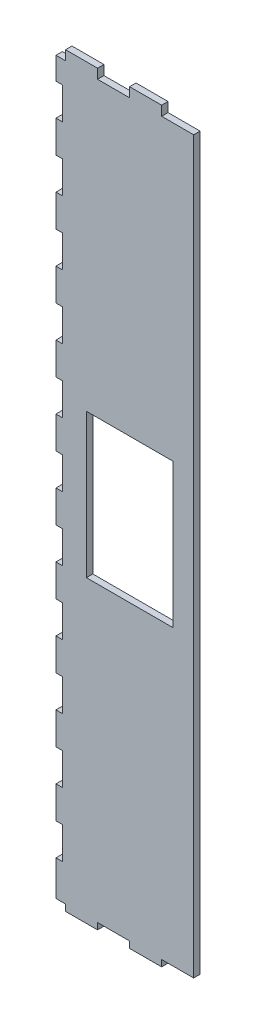
SolidWorks part; units mm, degrees
ref_plane "Front Plane" through (0, 0, 0) normal (0, 0, 1) x (1, 0, 0)
ref_plane "Top Plane" through (0, 0, 0) normal (0, 1, 0) x (1, 0, 0)
ref_plane "Right Plane" through (0, 0, 0) normal (1, 0, 0) x (0, 0, -1)
sketch "Sketch1" plane through (0, 0, 0) normal (0, 0, 1) x (1, 0, 0)
  line L1 (0, 0) -> (40, 0)
  line L2 (0, 0) -> (0, 227)
  line L3 (0, 227) -> (40, 227)
  line L4 (40, 0) -> (40, 227)
  dimension "D1" = 40
  dimension "D2" = 227
extrude "Boss-Extrude1" add sketch "Sketch1" along normal blind 2
sketch "Sketch2" plane through (0, 0, 0) normal (0, -1, 0) x (1, 0, 0)
  line L0 (0, 0) -> (40, 0) construction
  line L1 (30, 0) -> (20, 0)
  line L2 (30, 0) -> (30, 2)
  line L3 (30, 2) -> (20, 2)
  line L4 (20, 0) -> (20, 2)
  line L5 (0, 2) -> (40, 2) construction
  line L6 (40, 2) -> (40, 0) construction
  dimension "D1" = 10
  dimension "D2" = 10
extrude "Boss-Extrude2" add sketch "Sketch2" along normal blind 3
pattern_linear "LPattern1" count 2 spacing 20 along (-1, 0, 0) of "Boss-Extrude2"
sketch "Sketch3" plane through (0, 227, 0) normal (0, 1, 0) x (1, 0, 0)
  line L0 (40, -2) -> (0, -2) construction
  line L1 (30, -2) -> (20, -2)
  line L2 (30, -2) -> (30, 0)
  line L3 (30, 0) -> (20, 0)
  line L4 (20, -2) -> (20, 0)
  line L5 (40, 0) -> (0, 0) construction
  line L6 (40, -2) -> (40, 0) construction
  point P10 (40, -1)
  dimension "D1" = 10
  dimension "D2" = 10
extrude "Boss-Extrude3" add sketch "Sketch3" along normal blind 3
pattern_linear "LPattern2" count 2 spacing 20 along (-1, 0, 0) of "Boss-Extrude3"
sketch "Sketch4" plane through (0, 0, 0) normal (-1, 0, 0) x (0, 0, 1)
  line L0 (2, 230) -> (2, -3) construction
  line L1 (0, 0) -> (2, 0)
  line L2 (0, 0) -> (0, 10)
  line L3 (0, 10) -> (2, 10)
  line L4 (2, 0) -> (2, 10)
  dimension "D1" = 10
extrude "Boss-Extrude4" add sketch "Sketch4" along normal blind 3
pattern_linear "LPattern3" count 12 spacing 20 along (0, 1, 0) of "Boss-Extrude4"
sketch "Esquisse1" plane through (0, 0, 2) normal (0, 0, 1) x (1, 0, 0)
  line L1 (-3, 230) -> (0, 230)
  line L2 (-3, 230) -> (-3, 227)
  line L3 (-3, 227) -> (0, 227)
  line L4 (0, 230) -> (0, 227)
  dimension "D1" = 3
  dimension "D2" = 3
extrude "Enlèv. mat.-Extru.1" cut sketch "Esquisse1" against normal through all
sketch "Esquisse2" plane through (0, 0, 2) normal (0, 0, 1) x (1, 0, 0)
  line L0 (-3, 0) -> (0, 0) construction
  line L1 (0, 227) -> (-1, 227)
  line L2 (0, 227) -> (0, 0)
  line L3 (0, 0) -> (-1, 0)
  line L4 (-1, 227) -> (-1, 0)
  line L10 (-3, 0) -> (40, 0)
  line L11 (-3, 0) -> (-3, -1)
  line L12 (-3, -1) -> (40, -1)
  line L13 (40, 0) -> (40, -1)
  dimension "D1" = 1
  dimension "D2" = 1
extrude "Boss.-Extru.1" add sketch "Esquisse2" against normal blind 2 contours L11 L12 L13 L10 | L3 L4 L1 L2
sketch "Esquisse4" plane through (0, 0, 2) normal (0, 0, 1) x (1, 0, 0)
  line L0 (40, 227) -> (0, 227) construction
  line L1 (0, 227) -> (0, -1) construction
  line L2 (0, -1) -> (40, -1) construction
  line L3 (40, -1) -> (0, 227) construction
  line L4 (40, 227) -> (0, -1) construction
  line L6 (6.5, 135.5) -> (33.5, 135.5)
  line L7 (6.5, 135.5) -> (6.5, 90.5)
  line L8 (6.5, 90.5) -> (33.5, 90.5)
  line L9 (33.5, 135.5) -> (33.5, 90.5)
  line L10 (6.5, 135.5) -> (33.5, 90.5) construction
  line L11 (6.5, 90.5) -> (33.5, 135.5) construction
  point P4 (20, 113)
  dimension "D1" = 27
  dimension "D2" = 45
extrude "Enlèv. mat.-Extru.2" cut sketch "Esquisse4" against normal blind 3
